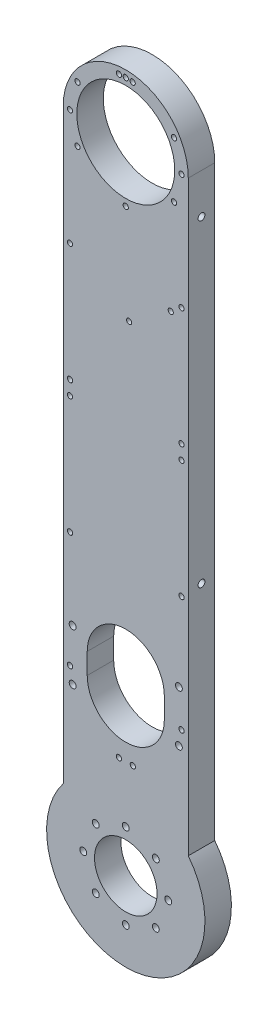
SolidWorks part; units mm, degrees
ref_plane "Front Plane" through (0, 0, 0) normal (0, 0, 1) x (1, 0, 0)
ref_plane "Top Plane" through (0, 0, 0) normal (0, 1, 0) x (1, 0, 0)
ref_plane "Right Plane" through (0, 0, 0) normal (1, 0, 0) x (0, 0, -1)
ref_plane "Plane1" through (0, 0, 12.7) normal (0, 0, 1) x (1, 0, 0)
sketch "Sketch1" plane through (0, 0, 12.7) normal (0, 0, 1) x (1, 0, 0)
  line L0 (-30, 305) -> (-30, 23.3238)
  line L1 (30, 23.3238) -> (30, 305)
  arc A0 (30, 305) -> (-30, 305) centre (0, 305) ccw
  arc A1 (-30, 23.3238) -> (30, 23.3238) centre (0, 0) ccw
extrude "Boss-Extrude1" add sketch "Sketch1" against normal blind 12.7
sketch "Sketch2" plane through (0, 0, 0) normal (0, 0, -1) x (-1, 0, 0)
  line L0 (18.5, 74.0225) -> (18.5, 84.0225)
  line L1 (-18.5, 84.0225) -> (-18.5, 74.0225)
  arc A0 (18.5, 84.0225) -> (-18.5, 84.0225) centre (0, 84.0225) ccw
  arc A1 (-18.5, 74.0225) -> (18.5, 74.0225) centre (0, 74.0225) ccw
extrude "Cut-Extrude1" cut sketch "Sketch2" against normal through all
hole_wizard "Hole1" positions "Sketch4" profile "Sketch3" legacy
sketch "Sketch4" plane through (0, 0, 12.7) normal (0, 0, 1) x (1, 0, 0)
  point P0 (0, 0)
sketch "Sketch3" plane through (0, 0, 12.7) normal (1, 0, 0) x (0, -1, 0)
  line L0 (0, 0) -> (0, 12.7)
  line L1 (0, 12.7) -> (15, 12.7)
  line L2 (15, 12.7) -> (15, 0)
  line L3 (15, 0) -> (0, 0)
  line L4 (0, 110) -> (0, -10) construction
  dimension "Diameter" = 30
  dimension "Depth" = 12.7
hole_wizard "Hole2" positions "Sketch6" profile "Sketch5" legacy
sketch "Sketch6" plane through (0, 0, 12.7) normal (0, 0, 1) x (1, 0, 0)
  point P0 (0, 305)
sketch "Sketch5" plane through (0, 305, 12.7) normal (1, 0, 0) x (0, -1, 0)
  line L0 (0, 0) -> (0, 12.7)
  line L1 (0, 12.7) -> (23.5, 12.7)
  line L2 (23.5, 12.7) -> (23.5, 0)
  line L3 (23.5, 0) -> (0, 0)
  line L4 (0, 110) -> (0, -10) construction
  dimension "Diameter" = 47
  dimension "Depth" = 12.7
hole_wizard "#39 (0.0995) Diameter Hole1" positions "Sketch8" profile "Sketch7" hole size "#39" standard "ANSI Inch"
sketch "Sketch8" plane through (0, 0, 12.7) normal (0, 0, 1) x (1, 0, 0)
  point P0 (-26.75, 74.0225)
  point P1 (-26.75, 129.5112)
  point P2 (-26.75, 186.1112)
  point P3 (-26.75, 192.9112)
  point P4 (-26.75, 249.5112)
  point P5 (-26.75, 305)
  point P6 (-3.3, 331.5457)
  point P7 (3.3, 331.5457)
  point P8 (26.75, 305)
  point P9 (26.75, 249.5112)
  point P10 (26.75, 192.9112)
  point P11 (26.75, 186.1112)
  point P12 (26.75, 129.5112)
  point P13 (26.75, 74.0225)
  point P14 (3.4, 47.4894)
  point P15 (-3.3, 47.4768)
  point P16 (-23.1662, 318.375)
  point P17 (-23.1662, 291.625)
  point P18 (0, 278.25)
  point P19 (23.1662, 291.625)
  point P20 (23.1662, 318.375)
  point P21 (0, 331.75)
sketch "Sketch7" plane through (-26.75, 74.0225, 12.7) normal (1, 0, 0) x (0, -1, 0)
  line L0 (0, 0) -> (0, 12.7)
  line L1 (0, 12.7) -> (1.2636, 12.7)
  line L2 (1.2636, 12.7) -> (1.2636, 0)
  line L5 (1.2636, 0) -> (0, 0)
  line L11 (0, -6.35) -> (0, 107.95) construction
  dimension "Thru Hole Dia." = 2.5273
  dimension "Thru Hole Depth" = 12.7
hole_wizard "#4 Clearance Hole1" positions "Sketch10" profile "Sketch9" hole size "#4" standard "ANSI Inch"
sketch "Sketch10" plane through (0, 0, 0) normal (0, 0, -1) x (-1, 0, 0)
  line L0 (0, 102.5225) -> (0, 55.5225) construction
  arc A0 (18.5, 84.0225) -> (-18.5, 84.0225) centre (0, 84.0225) ccw construction
  arc A1 (-18.5, 74.0225) -> (18.5, 74.0225) centre (0, 74.0225) ccw construction
  point P2 (-25.5016, 66.7725)
  point P3 (-25.5016, 91.2725)
  point P4 (14.425, 14.425)
  point P5 (20.4, 0)
  point P6 (14.425, -14.425)
  point P7 (0, -20.4)
  point P8 (-14.425, -14.425)
  point P9 (-20.4, 0)
  point P10 (-14.425, 14.425)
  point P11 (0, 20.4)
  point P25 (25.5016, 66.7725)
  point P26 (25.5016, 91.2725)
  point P27 (0, 79.0225)
  dimension "D1" = 25.5016
  dimension "D2" = 25.5016
  dimension "D3" = 12.25
  dimension "D4" = 12.25
sketch "Sketch9" plane through (25.5016, 66.7725, 0) normal (1, 0, 0) x (0, 1, 0)
  line L0 (0, 0) -> (0, 12.7)
  line L1 (0, 12.7) -> (1.65, 12.7)
  line L2 (1.65, 12.7) -> (1.65, 0)
  line L5 (1.65, 0) -> (0, 0)
  line L11 (0, -6.35) -> (0, 107.95) construction
  dimension "Thru Hole Dia." = 3.3
  dimension "Thru Hole Depth" = 12.7
hole_wizard "#2 Clearance Hole1" positions "Sketch12" profile "Sketch11" hole size "#2" standard "ANSI Inch"
sketch "Sketch12" plane through (0, 0, 0) normal (0, 0, -1) x (-1, 0, 0)
  point P0 (-1.6199, 231.2653)
  point P1 (-21.5789, 245.4337)
sketch "Sketch11" plane through (1.6199, 231.2653, 0) normal (1, 0, 0) x (0, 1, 0)
  line L0 (0, 0) -> (0, 12.7)
  line L1 (0, 12.7) -> (1.25, 12.7)
  line L2 (1.25, 12.7) -> (1.25, 0)
  line L5 (1.25, 0) -> (0, 0)
  line L11 (0, -6.35) -> (0, 107.95) construction
  dimension "Thru Hole Dia." = 2.5
  dimension "Thru Hole Depth" = 12.7
hole_wizard "#4 Clearance Hole2" positions "Sketch14" profile "Sketch13" hole size "#4" standard "ANSI Inch"
sketch "Sketch14" plane through (30, 0, 0) normal (1, 0, 0) x (0, 0, -1)
  point P0 (-6.35, 285.7238)
  point P1 (-6.35, 133.3238)
sketch "Sketch13" plane through (30, 285.7238, 6.35) normal (0, 1, 0) x (0, 0, -1)
  line L0 (0, 0) -> (0, 10)
  line L1 (0, 10) -> (1.65, 10)
  line L2 (1.65, 10) -> (1.65, 0)
  line L5 (1.65, 0) -> (0, 0)
  line L10 (0, 10) -> (-1.65, 10) construction
  line L11 (0, -6.35) -> (0, 107.95) construction
  dimension "Hole Dia." = 3.3
  dimension "Hole Depth" = 10
  dimension "Drill Angle" = 180
